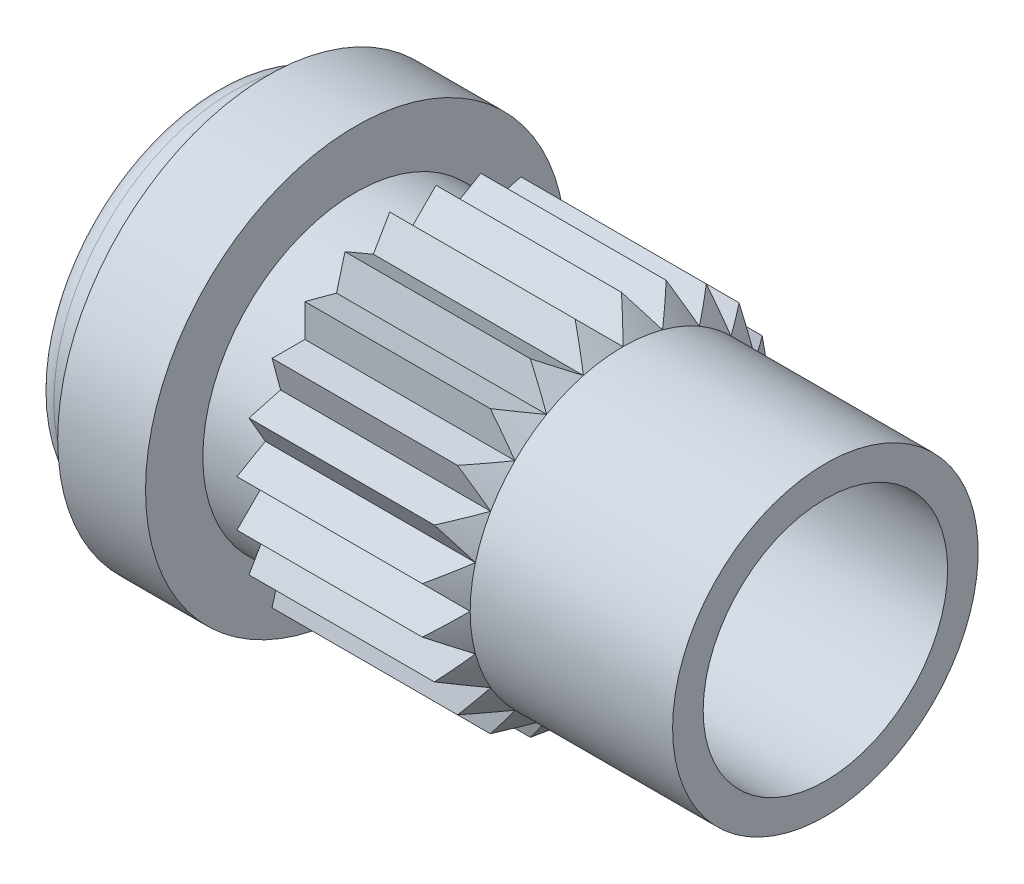
SolidWorks part; units mm, degrees
material "Brass Alloy 360"
ref_plane "Front Plane" through (0, 0, 0) normal (0, 0, 1) x (1, 0, 0)
ref_plane "Top Plane" through (0, 0, 0) normal (0, 1, 0) x (1, 0, 0)
ref_plane "Right Plane" through (0, 0, 0) normal (1, 0, 0) x (0, 0, -1)
sketch "Sketch1" plane through (0, 0, 0) normal (0, 0, 1) x (1, 0, 0)
  line L0 (4.064, 0) -> (4.064, 1.016)
  line L1 (4.064, 1.016) -> (2.7178, 1.016)
  line L2 (2.7178, 1.016) -> (2.5527, 1.1811)
  line L3 (2.5527, 1.1811) -> (1.3208, 1.1811)
  line L4 (1.3208, 1.1811) -> (1.3208, 1.016)
  line L5 (0.9398, 1.016) -> (1.3208, 1.016)
  line L6 (0.9398, 1.397) -> (0.9398, 1.016)
  line L7 (0.3556, 1.397) -> (0.9398, 1.397)
  line L8 (0.3556, 1.1938) -> (0.3556, 1.397)
  line L9 (0.127, 1.1938) -> (0.3556, 1.1938)
  line L10 (0, 0) -> (0, 1.0668)
  line L11 (0, 0) -> (4.064, 0)
  line L12 (0, 0) -> (4.064, 0) construction
  arc A0 (0.127, 1.1938) -> (0, 1.0668) centre (0.127, 1.0668) ccw
revolve "RevolutionAngle1" add sketch "Sketch1" angle 360 about L12
hole_wizard "Hole1" positions "Sketch3" profile "Sketch2" legacy end condition through all
sketch "Sketch3" plane through (0, 0, 0) normal (-1, 0, 0) x (0, 0, 1)
  point P0 (0, 0)
sketch "Sketch2" plane through (0, 0, 0) normal (0, 1, 0) x (0, 0, 1)
  line L0 (0, 0) -> (0, 4.5524)
  line L1 (0, 4.5524) -> (0.8128, 4.064)
  line L2 (0.8128, 4.064) -> (0.8128, 0)
  line L4 (0.8128, 0) -> (0, 0)
  line L6 (0, 4.5524) -> (-0.8128, 4.064) construction
  line L7 (0, -4.2442) -> (0, 117.3081) construction
  dimension "Diameter" = 1.6256
  dimension "Depth" = 4.064
  dimension "Drill Angle" = 118
sketch "Sketch4" plane through (1.3208, 0, 0) normal (-1, 0, 0) x (0, 0, 1)
  line L0 (-1.016, 0) -> (-1.1811, -0.1651)
  line L1 (-1.1811, -0.1651) -> (-1.1811, 0.1651)
  line L2 (-1.016, 0) -> (-1.1811, 0.1651)
  circle A0 centre (0, 0) radius 0.8128 construction
  dimension "D4" = 0.1651
  dimension "D1" = 1.1811
  dimension "D2" = 1.016
  dimension "D3" = 0.3302
extrude "ExtrusionBlind1" cut sketch "Sketch4" against normal blind 1.397
pattern_circular "Polar Pattern1" count 24 over 360 about axis through (0, 0, 0) along (1, 0, 0) of "ExtrusionBlind1"
